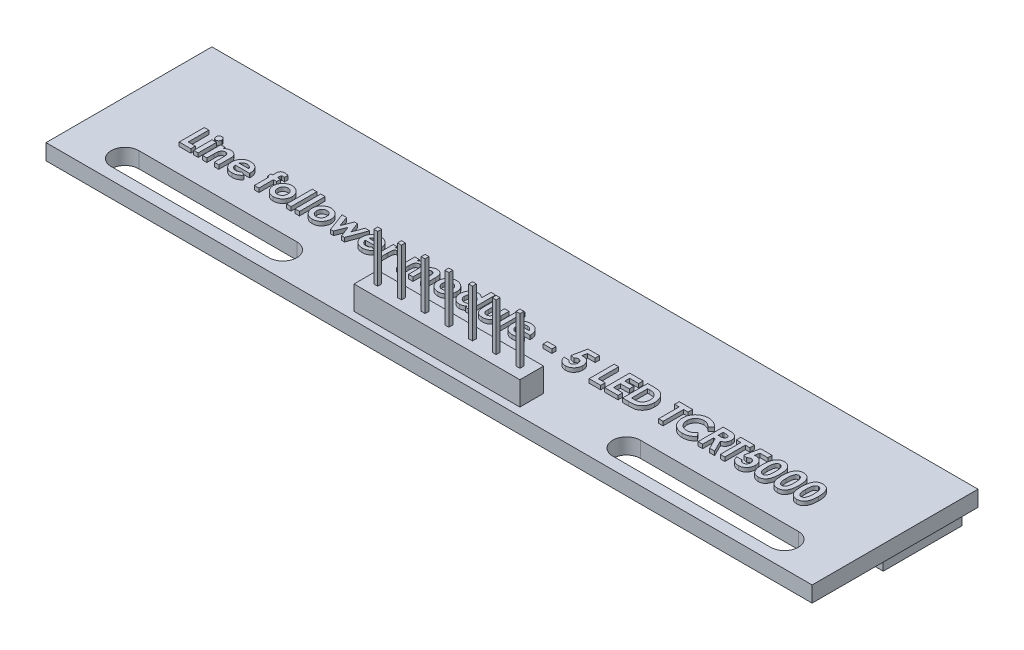
SolidWorks part; units mm, degrees
ref_plane "Front Plane" through (0, 0, 0) normal (0, 0, 1) x (1, 0, 0)
ref_plane "Top Plane" through (0, 0, 0) normal (0, 1, 0) x (1, 0, 0)
ref_plane "Right Plane" through (0, 0, 0) normal (1, 0, 0) x (0, 0, -1)
sketch "Base" plane through (0, 0, 0) normal (0, 1, 0) x (1, 0, 0)
  line L0 (-34.9038, -7.4265) -> (-14.9038, -7.4265) construction
  line L1 (-41.6538, 10.3235) -> (55.3462, 10.3235)
  line L2 (-41.6538, 10.3235) -> (-41.6538, -10.6765)
  line L3 (-41.6538, -10.6765) -> (55.3462, -10.6765)
  line L4 (55.3462, 10.3235) -> (55.3462, -10.6765)
  line L5 (-41.6538, 10.3235) -> (55.3462, -10.6765) construction
  line L6 (-41.6538, -10.6765) -> (55.3462, 10.3235) construction
  line L7 (48.5962, -7.4265) -> (28.5962, -7.4265) construction
  line L8 (-34.9038, -5.6765) -> (-14.9038, -5.6765)
  line L9 (-34.9038, -9.1765) -> (-14.9038, -9.1765)
  line L10 (48.5962, -9.1765) -> (28.5962, -9.1765)
  line L11 (48.5962, -5.6765) -> (28.5962, -5.6765)
  arc A0 (-34.9038, -5.6765) -> (-34.9038, -9.1765) centre (-34.9038, -7.4265) ccw
  arc A1 (-14.9038, -9.1765) -> (-14.9038, -5.6765) centre (-14.9038, -7.4265) ccw
  arc A2 (48.5962, -9.1765) -> (48.5962, -5.6765) centre (48.5962, -7.4265) ccw
  arc A3 (28.5962, -5.6765) -> (28.5962, -9.1765) centre (28.5962, -7.4265) ccw
  point P0 (6.8462, -0.1765)
  point P7 (-36.6538, -7.4265)
  point P9 (-24.9038, -7.4265)
  point P15 (38.5962, -7.4265)
  point P20 (50.3462, -7.4265)
  dimension "D1" = 21
  dimension "D2" = 97
  dimension "D3" = 5
  dimension "D4" = 1.5
  dimension "D5" = 5
  dimension "D6" = 1.5
extrude "Base circuit" add sketch "Base" along normal blind 2
sketch "Sketch3" plane through (0, 2, 0) normal (0, 1, 0) x (1, 0, 0)
  line L0 (-41.6538, -10.6765) -> (55.3462, -10.6765) construction
  line L1 (-3.6538, -6.6765) -> (-0.6538, -6.6765)
  line L2 (-3.6538, -6.6765) -> (-3.6538, -9.6765)
  line L3 (-3.6538, -9.6765) -> (-0.6538, -9.6765)
  line L4 (-0.6538, -6.6765) -> (-0.6538, -9.6765)
  line L5 (-3.6538, -6.6765) -> (-0.6538, -9.6765) construction
  line L6 (-3.6538, -9.6765) -> (-0.6538, -6.6765) construction
  line L7 (-41.6538, 10.3235) -> (-41.6538, -10.6765) construction
  point P0 (-2.1538, -8.1765)
  point P9 (-3.6538, -8.1765)
  dimension "D1" = 3
  dimension "D2" = 1
  dimension "D3" = 38
extrude "Pin foot" add sketch "Sketch3" along normal blind 3
sketch "Sketch4" plane through (0, 5, 0) normal (0, 1, 0) x (1, 0, 0)
  line L1 (-2.4038, -7.9265) -> (-1.9038, -7.9265)
  line L2 (-2.4038, -7.9265) -> (-2.4038, -8.4265)
  line L3 (-2.4038, -8.4265) -> (-1.9038, -8.4265)
  line L4 (-1.9038, -7.9265) -> (-1.9038, -8.4265)
  line L5 (-2.4038, -7.9265) -> (-1.9038, -8.4265) construction
  line L6 (-2.4038, -8.4265) -> (-1.9038, -7.9265) construction
  line L7 (-0.6538, -6.6765) -> (-3.6538, -6.6765) construction
  line L8 (-0.6538, -9.6765) -> (-0.6538, -6.6765) construction
  point P0 (-2.1538, -8.1765)
  dimension "D1" = 0.5
  dimension "D2" = 1.25
  dimension "D3" = 1.25
extrude "Pin" add sketch "Sketch4" along normal blind 6
pattern_linear "LPattern1" count 7 spacing 3 along (1, 0, 0) of "Pin foot"
pattern_linear "LPattern2" count 7 spacing 3 along (1, 0, 0) of "Pin"
sketch "Sketch5" plane through (0, 0, 0) normal (0, -1, 0) x (-1, 0, 0)
  line L0 (41.6538, 10.3235) -> (41.6538, -10.6765) construction
  line L1 (40.6538, 0.3235) -> (34.6538, 0.3235)
  line L2 (40.6538, 0.3235) -> (40.6538, 10.3235)
  line L3 (40.6538, 10.3235) -> (34.6538, 10.3235)
  line L4 (34.6538, 0.3235) -> (34.6538, 10.3235)
  line L5 (40.6538, 0.3235) -> (34.6538, 10.3235) construction
  line L6 (40.6538, 10.3235) -> (34.6538, 0.3235) construction
  line L7 (-55.3462, 10.3235) -> (41.6538, 10.3235) construction
  point P0 (37.6538, 5.3235)
  dimension "D1" = 10
  dimension "D2" = 6
  dimension "D3" = 1
  dimension "D4" = 0
extrude "Boss-Extrude4" add sketch "Sketch5" along normal blind 4
chamfer "Chamfer2" distance 1 angle 45 4 edges at (-37.6538, -4, -0.3235) (-40.6538, -4, -5.3235) (-37.6538, -4, -10.3235) (-34.6538, -4, -5.3235)
pattern_linear "LPattern9" count 5 spacing 22 along (1, 0, 0) of "Boss-Extrude4", "Chamfer2"
sketch "Sketch8" plane through (0, 2, 0) normal (0, 1, 0) x (1, 0, 0)
  line L0 (-33.1538, -2.6765) -> (46.8462, -2.6765) construction
  line L1 (-41.6538, 10.3235) -> (-41.6538, -10.6765) construction
  line L2 (-41.6538, -10.6765) -> (55.3462, -10.6765) construction
  text T0 "<b>Line follower module - 5 LED TCRT5000</b>"
  point P4 (0, 0)
  point P5 (0, 0)
  dimension "D1" = 8.5
  dimension "D3" = 8
extrude "Boss-Extrude5" add sketch "Sketch8" along normal blind 0.5
equation "\"D5@Base\"=\"D3@Base\""
equation "\"D6@Base\"=\"D4@Base\""
equation "\"D2@Sketch4\"=(\"D1@Sketch3\"-\"D1@Sketch4\")/2"
equation "\"D3@Sketch4\"=\"D2@Sketch4\""
equation "\"D3@Sketch3\"=(\"D2@Base\"-3*7)/2"
equation "\"D1@Sketch8\"=(\"D2@Base\"-80)/2"
